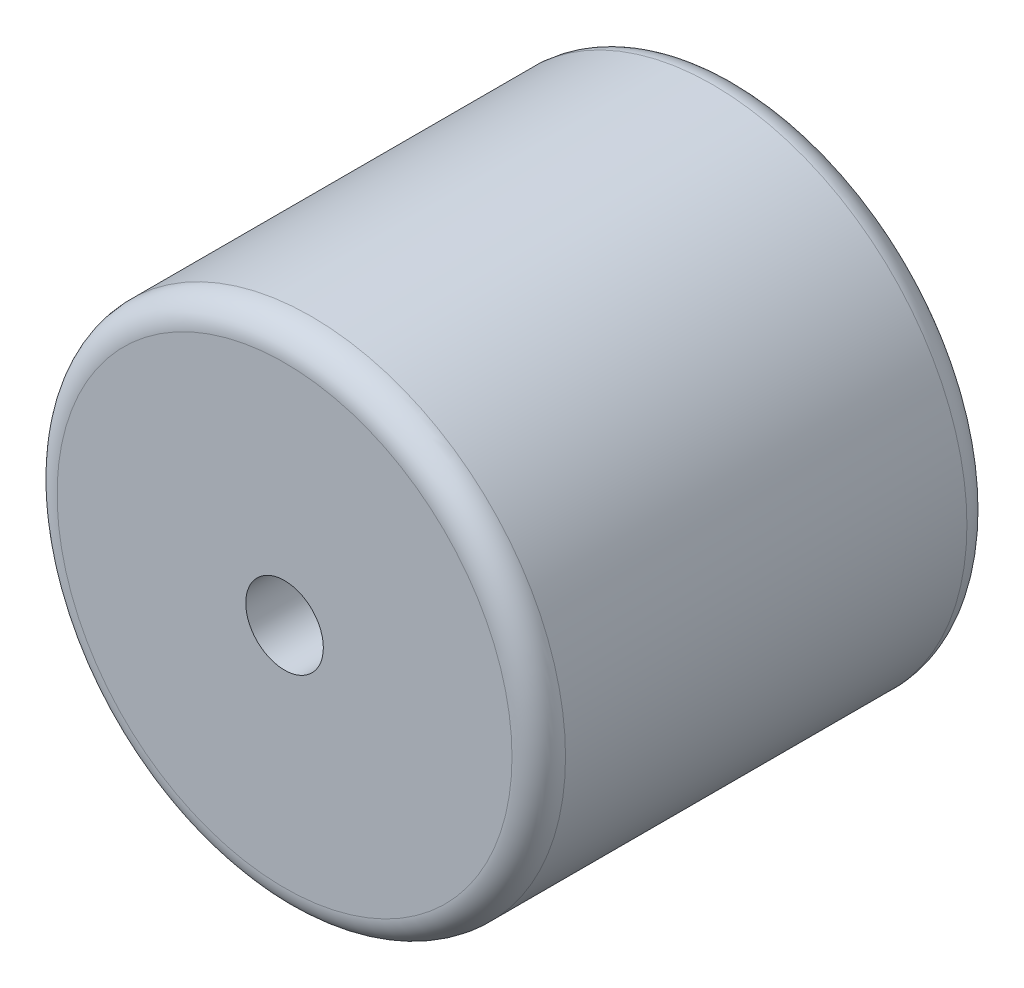
SolidWorks part; units mm, degrees
material "BUTYL"
ref_plane "Front Plane" through (0, 0, 0) normal (0, 0, 1) x (1, 0, 0)
ref_plane "Top Plane" through (0, 0, 0) normal (0, 1, 0) x (1, 0, 0)
ref_plane "Right Plane" through (0, 0, 0) normal (1, 0, 0) x (0, 0, -1)
sketch "Sketch1" plane through (0, 0, 0) normal (0, 0, 1) x (1, 0, 0)
  circle A0 centre (0, 0) radius 9.5
  dimension "D1" = 19
extrude "Boss-Extrude1" add sketch "Sketch1" along normal blind 17
fillet "Fillet1" radius 1 2 edges at (9.5, 0, 0) (9.5, 0, 17)
sketch "Sketch2" plane through (0, 0, 17) normal (0, 0, 1) x (1, 0, 0)
  circle A0 centre (0, 0) radius 1.45
  dimension "D1" = 2.9
extrude "Cut-Extrude1" cut sketch "Sketch2" against normal blind 17
